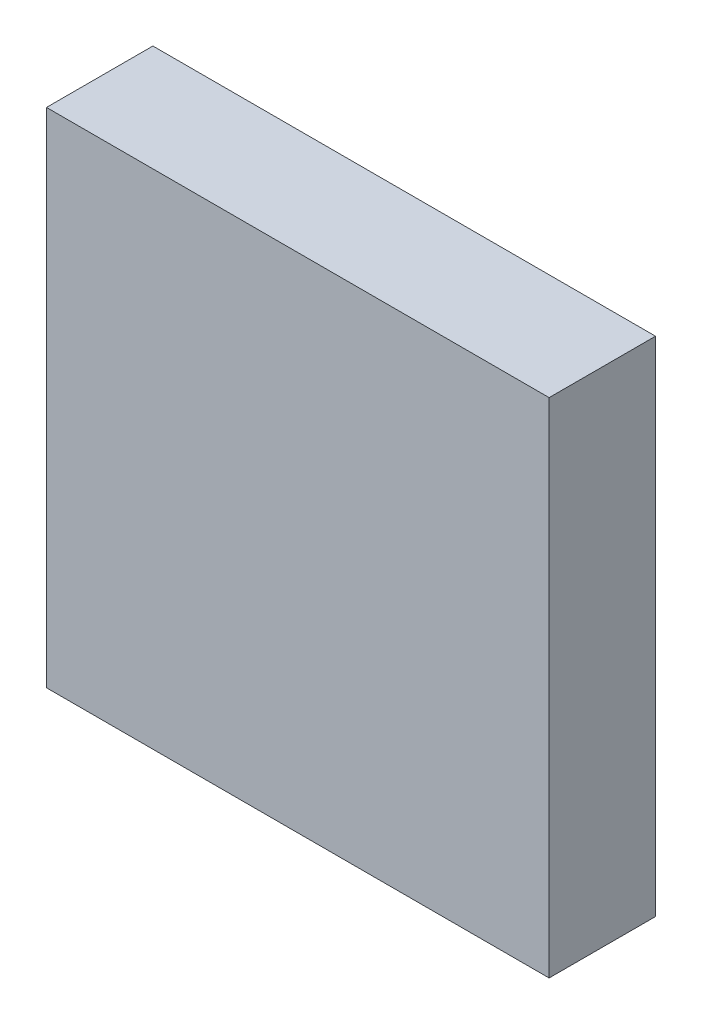
SolidWorks part; units mm, degrees
material "Balsa"
ref_plane "Front Plane" through (0, 0, 0) normal (0, 0, 1) x (1, 0, 0)
ref_plane "Top Plane" through (0, 0, 0) normal (0, 1, 0) x (1, 0, 0)
ref_plane "Right Plane" through (0, 0, 0) normal (1, 0, 0) x (0, 0, -1)
sketch "Sketch1" plane through (0, 0, 0) normal (0, 0, 1) x (1, 0, 0)
  line L1 (0, 0) -> (30, 0)
  line L2 (0, 0) -> (0, 30)
  line L3 (0, 30) -> (30, 30)
  line L4 (30, 0) -> (30, 30)
  dimension "D1" = 30
  dimension "D2" = 30
extrude "Boss-Extrude1" add sketch "Sketch1" along normal blind 6.35
